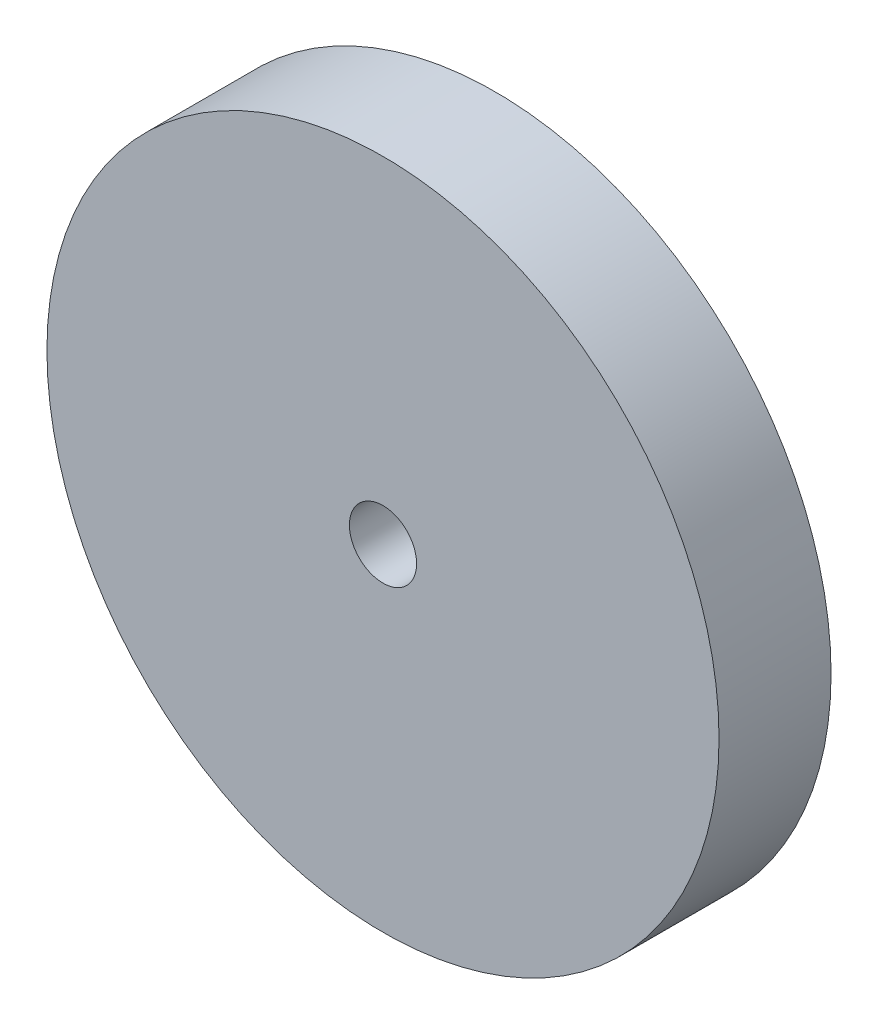
SolidWorks part; units mm, degrees
ref_plane "Front Plane" through (0, 0, 0) normal (0, 0, 1) x (1, 0, 0)
ref_plane "Top Plane" through (0, 0, 0) normal (0, 1, 0) x (1, 0, 0)
ref_plane "Right Plane" through (0, 0, 0) normal (1, 0, 0) x (0, 0, -1)
sketch "Sketch1" plane through (0, 0, 0) normal (0, 0, 1) x (1, 0, 0)
  circle A0 centre (0, 0) radius 60
  dimension "D1" = 120
extrude "Boss-Extrude2" add sketch "Sketch1" along normal blind 20
sketch "Sketch2" plane through (0, 0, 20) normal (0, 0, 1) x (1, 0, 0)
  circle A0 centre (0, 0) radius 6
  circle A1 centre (0, 0) radius 60 construction
  dimension "D1" = 12
extrude "Cut-Extrude1" cut sketch "Sketch2" against normal through all
